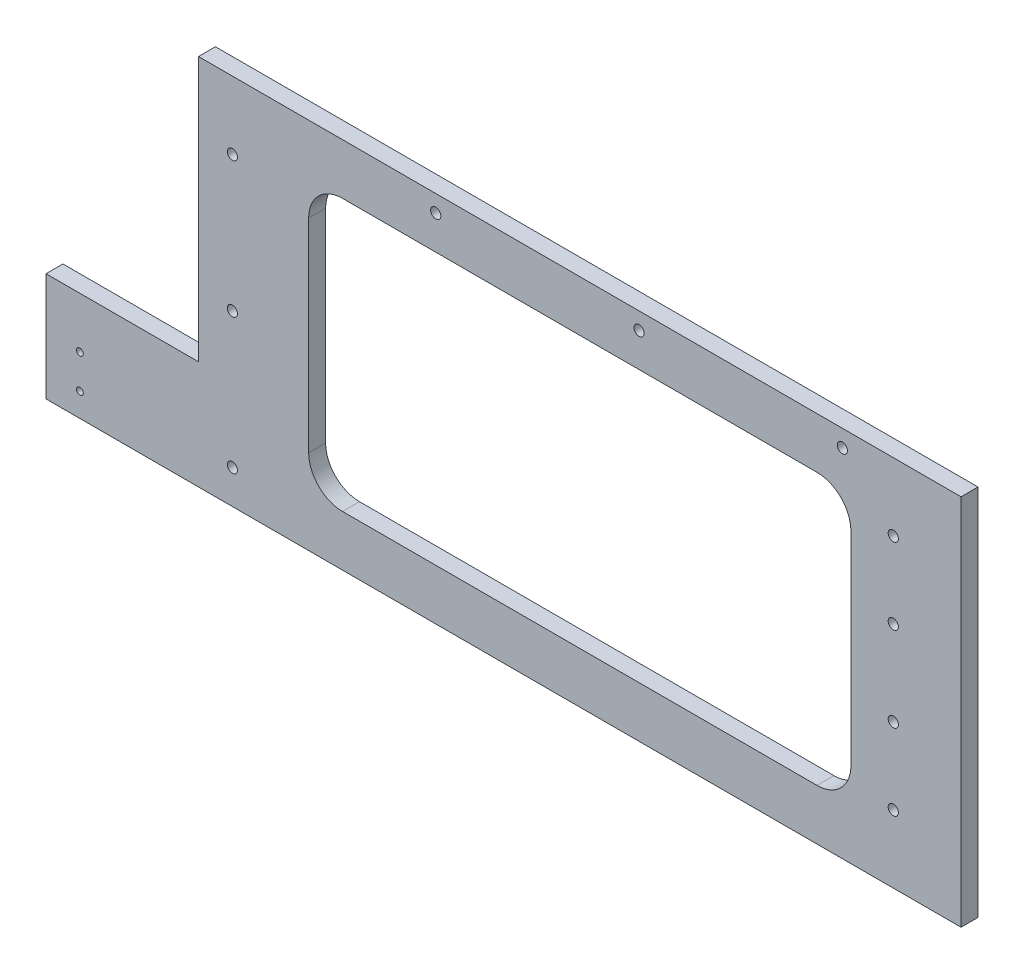
SolidWorks part; units mm, degrees
material "Polywood"
ref_plane "Front Plane" through (0, 0, 0) normal (0, 0, 1) x (1, 0, 0)
ref_plane "Top Plane" through (0, 0, 0) normal (0, 1, 0) x (1, 0, 0)
ref_plane "Right Plane" through (0, 0, 0) normal (1, 0, 0) x (0, 0, -1)
sketch "Sketch1" plane through (0, 0, 0) normal (0, 0, 1) x (1, 0, 0)
  line L1 (112.5, -55) -> (-112.5, -55)
  line L2 (112.5, -55) -> (112.5, 55)
  line L3 (112.5, 55) -> (-112.5, 55)
  line L4 (-112.5, -55) -> (-112.5, 55)
  line L5 (112.5, -55) -> (-112.5, 55) construction
  line L6 (112.5, 55) -> (-112.5, -55) construction
  point P0 (0, 0)
  dimension "D1" = 110
  dimension "D2" = 225
extrude "Boss-Extrude1" add sketch "Sketch1" along normal blind 5
sketch "Sketch2" plane through (-112.5, 0, 0) normal (-1, 0, 0) x (0, 0, 1)
  line L0 (5, 55) -> (5, -55) construction
  line L1 (0, -55) -> (5, -55)
  line L2 (0, -55) -> (0, -23)
  line L3 (0, -23) -> (5, -23)
  line L4 (5, -55) -> (5, -23)
  dimension "D1" = 32
extrude "Boss-Extrude2" add sketch "Sketch2" along normal blind 45
sketch "Sketch3" plane through (0, 0, 5) normal (0, 0, 1) x (1, 0, 0)
  line L0 (112.5, 0) -> (50112.5, 0) construction
  line L1 (112.5, -55) -> (112.5, 55) construction
  line L2 (112.5, 55) -> (-112.5, 55) construction
  line L3 (98.8377, 23.75) -> (50098.8377, 23.75) construction
  circle A0 centre (92.5, 35) radius 1.5
  circle A1 centre (92.5, 12.5) radius 1.5
  circle A2 centre (92.5, 35) radius 1.5
  circle A3 centre (92.5, 12.5) radius 1.5
  circle A4 centre (92.5, -12.5) radius 1.5
  circle A5 centre (92.5, -35) radius 1.5
  circle A6 centre (92.5, -12.5) radius 1.5
  circle A7 centre (92.5, -35) radius 1.5
  point P4 (112.5, 0)
  dimension "D3" = 3
  dimension "D1" = 20
  dimension "D2" = 20
  dimension "D4" = 11.25
extrude "Cut-Extrude1" cut sketch "Sketch3" against normal through all contours A0 | A1 | A4 | A5
sketch "Sketch4" plane through (0, 0, 5) normal (0, 0, 1) x (1, 0, 0)
  line L0 (112.5, 55) -> (-112.5, 55) construction
  line L1 (-112.5, 55) -> (-112.5, -23) construction
  circle A0 centre (-42.5, 50) radius 1.5
  circle A1 centre (-102.5, 35) radius 1.5
  circle A2 centre (17.5, 50) radius 1.5
  circle A3 centre (77.5, 50) radius 1.5
  circle A4 centre (-102.5, -5) radius 1.5
  circle A5 centre (-102.5, -45) radius 1.5
  dimension "D3" = 3
  dimension "D1" = 5
  dimension "D2" = 70
  dimension "D4" = 20
  dimension "D5" = 10
  dimension "D6" = 3
  dimension "D7" = 3
extrude "Cut-Extrude2" cut sketch "Sketch4" against normal through all
sketch "Sketch5" plane through (0, 0, 5) normal (0, 0, 1) x (1, 0, 0)
  line L0 (-157.5, -55) -> (-157.5, -23) construction
  line L1 (-157.5, -23) -> (-112.5, -23) construction
  line L2 (-150.9271, -43) -> (49849.0729, -43) construction
  circle A0 centre (-147.5, -38) radius 1
  circle A1 centre (-147.5, -48) radius 1
  dimension "D1" = 2
  dimension "D2" = 10
  dimension "D3" = 15
  dimension "D4" = 5
extrude "Cut-Extrude3" cut sketch "Sketch5" against normal through all
sketch "Sketch6" plane through (0, 0, 5) normal (0, 0, 1) x (1, 0, 0)
  line L0 (112.5, 55) -> (-112.5, 55) construction
  line L1 (-80, 40) -> (80, 40)
  line L2 (-80, 40) -> (-80, -40)
  line L3 (-80, -40) -> (80, -40)
  line L4 (80, 40) -> (80, -40)
  dimension "D1" = 40
  dimension "D2" = 15
  dimension "D3" = 80
  dimension "D4" = 80
extrude "Cut-Extrude4" cut sketch "Sketch6" against normal through all
fillet "Fillet1" radius 10 4 edges at (80, 40, 2.5) (80, -40, 2.5) (-80, -40, 2.5) (-80, 40, 2.5)
